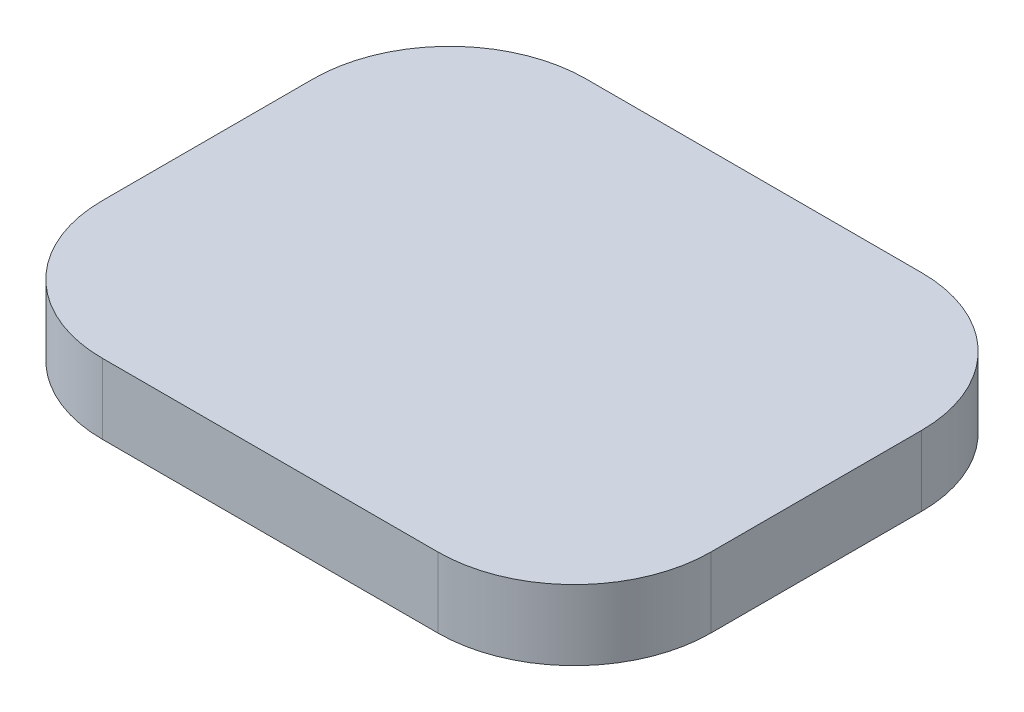
SolidWorks part; units mm, degrees
material "Cèdre"
ref_plane "Plan de face" through (0, 0, 0) normal (0, 0, 1) x (1, 0, 0)
ref_plane "Plan de dessus" through (0, 0, 0) normal (0, 1, 0) x (1, 0, 0)
ref_plane "Plan de droite" through (0, 0, 0) normal (1, 0, 0) x (0, 0, -1)
sketch "Esquisse1" plane through (0, 0, 0) normal (0, 1, 0) x (1, 0, 0)
  line L0 (-39, 0) -> (39, 0) construction
  line L1 (-39, 31) -> (39, 31)
  line L2 (-39, 31) -> (-39, -31)
  line L3 (-39, -31) -> (39, -31)
  line L4 (39, 31) -> (39, -31)
  dimension "D1" = 78
  dimension "D2" = 62
extrude "Boss.-Extru.1" add sketch "Esquisse1" along normal blind 9
fillet "Congé1" radius 17.5 4 edges at (-39, 4.5, -31) (39, 4.5, -31) (-39, 4.5, 31) (39, 4.5, 31)
